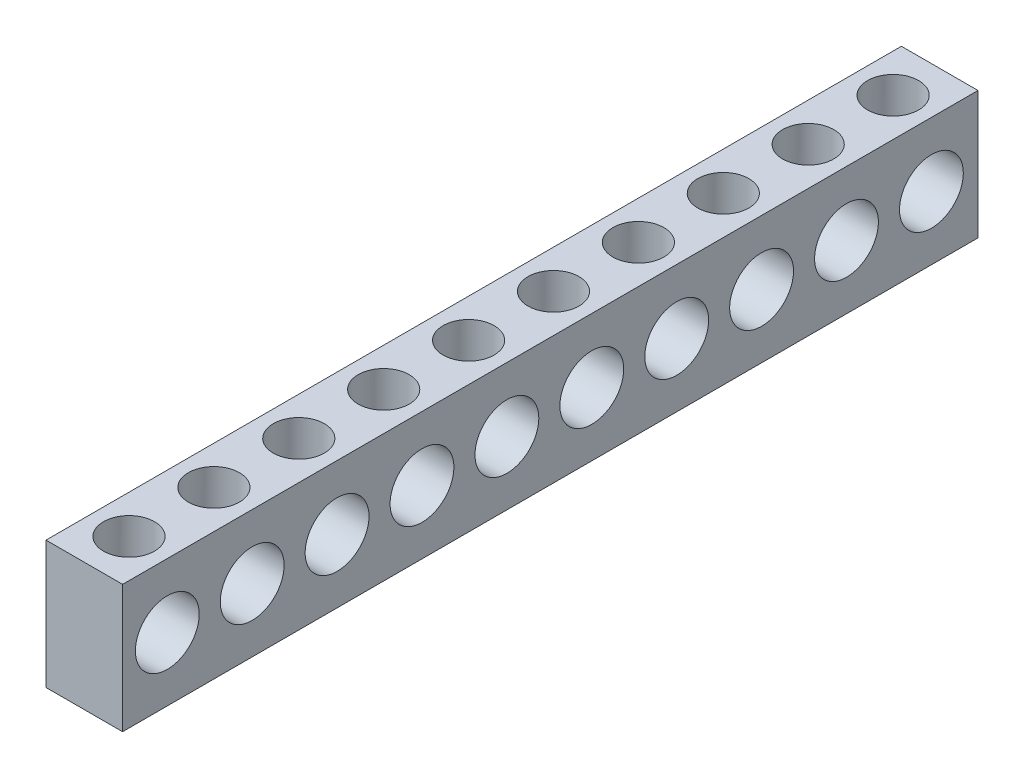
SolidWorks part; units mm, degrees
ref_plane "Plano frontal" through (0, 0, 0) normal (0, 0, 1) x (1, 0, 0)
ref_plane "Plano superior" through (0, 0, 0) normal (0, 1, 0) x (1, 0, 0)
ref_plane "Plano direito" through (0, 0, 0) normal (1, 0, 0) x (0, 0, -1)
sketch "Esboço1" plane through (0, 0, 0) normal (0, 0, 1) x (1, 0, 0)
  line L1 (0, 0) -> (-6, 0)
  line L2 (0, 0) -> (0, 10)
  line L3 (0, 10) -> (-6, 10)
  line L4 (-6, 0) -> (-6, 10)
  dimension "D1" = 10
  dimension "D2" = 6
extrude "Ressalto-extrusão1" add sketch "Esboço1" along normal blind 67
sketch "Esboço2" plane through (0, 0, 0) normal (1, 0, 0) x (0, 0, -1)
  line L0 (-67, 0) -> (-67, 10) construction
  circle A0 centre (-63.5, 4.9775) radius 2.5
  circle A1 centre (-56.85, 4.9775) radius 2.5
  circle A2 centre (-50.2, 4.9775) radius 2.5
  circle A3 centre (-43.55, 4.9775) radius 2.5
  circle A4 centre (-36.9, 4.9775) radius 2.5
  circle A5 centre (-30.25, 4.9775) radius 2.5
  circle A6 centre (-23.6, 4.9775) radius 2.5
  circle A7 centre (-16.95, 4.9775) radius 2.5
  circle A8 centre (-10.3, 4.9775) radius 2.5
  circle A9 centre (-3.65, 4.9775) radius 2.5
  point P3 (-63.4309, 4.9775)
  dimension "D1" = 5
  dimension "D3" = 3.5
  dimension "D2" = 10
extrude "Corte-extrusão1" cut sketch "Esboço2" against normal blind 67
sketch "Esboço3" plane through (0, 10, 0) normal (0, 1, 0) x (1, 0, 0)
  line L0 (0, -67) -> (-6, -67) construction
  circle A1 centre (-3, -63.5) radius 2
  circle A2 centre (-3, -56.85) radius 2
  circle A3 centre (-3, -50.2) radius 2
  circle A4 centre (-3, -43.55) radius 2
  circle A5 centre (-3, -36.9) radius 2
  circle A6 centre (-3, -30.25) radius 2
  circle A7 centre (-3, -23.6) radius 2
  circle A8 centre (-3, -16.95) radius 2
  circle A9 centre (-3, -10.3) radius 2
  circle A10 centre (-3, -3.65) radius 2
  dimension "D2" = 4
  dimension "D3" = 10
  dimension "D1" = 3.5
extrude "Corte-extrusão2" cut sketch "Esboço3" against normal blind 6
